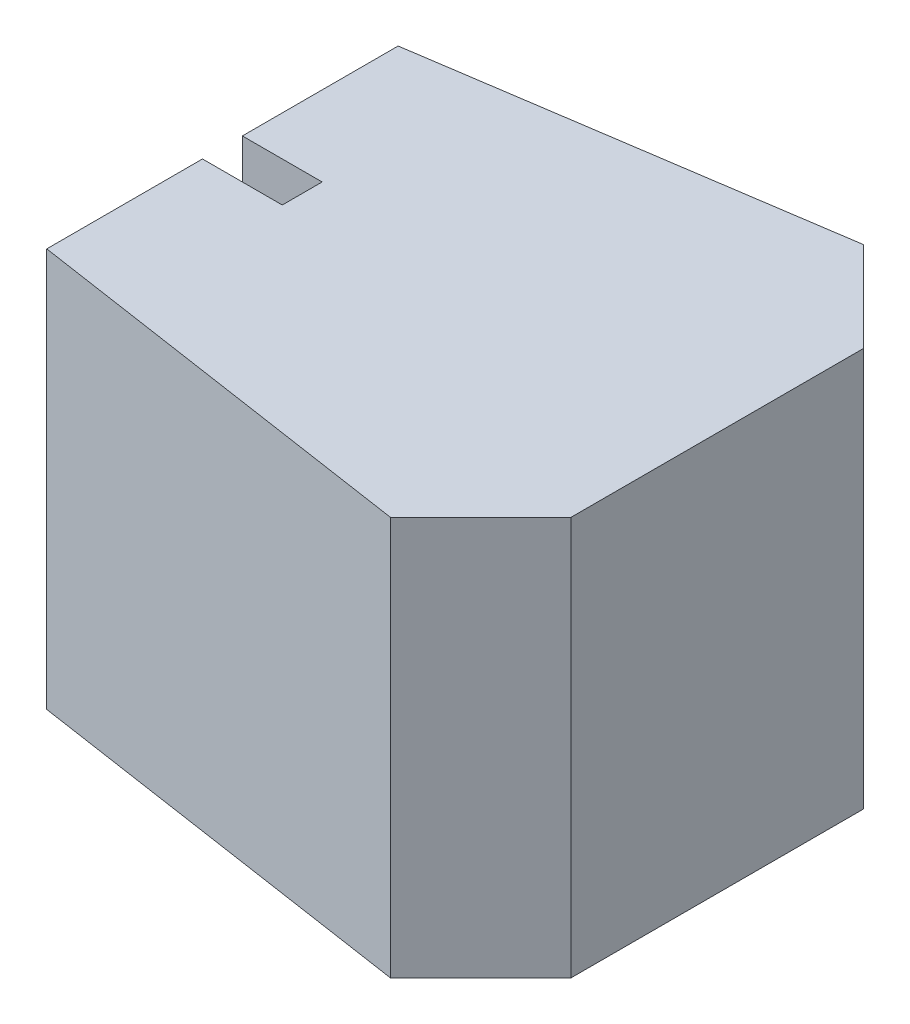
SolidWorks part; units mm, degrees
ref_plane "Front Plane" through (0, 0, 0) normal (0, 0, 1) x (1, 0, 0)
ref_plane "Top Plane" through (0, 0, 0) normal (0, 1, 0) x (1, 0, 0)
ref_plane "Right Plane" through (0, 0, 0) normal (1, 0, 0) x (0, 0, -1)
sketch "Sketch1" plane through (0, 0, 0) normal (0, 1, 0) x (1, 0, 0)
  line L0 (0, 0) -> (600, 0) construction
  line L1 (0, -200) -> (0, 200) construction
  line L2 (600, -175) -> (600, 175) construction
  line L3 (600, 175) -> (500, 275) construction
  line L4 (500, 275) -> (0, 200) construction
  line L5 (100, -25) -> (100, 25)
  line L6 (100, 25) -> (0, 25)
  line L7 (100, -25) -> (0, -25)
  line L8 (500, -275) -> (0, -200) construction
  line L9 (600, -175) -> (500, -275) construction
  line L10 (507.0092, -296.2751) -> (-20, -217.2237)
  line L11 (-20, -217.2237) -> (-20, 217.2237)
  line L12 (507.0092, 296.2751) -> (-20, 217.2237)
  line L13 (620, 183.2843) -> (507.0092, 296.2751)
  line L14 (620, -183.2843) -> (620, 183.2843)
  line L15 (620, -183.2843) -> (507.0092, -296.2751)
  line L16 (0, 200) -> (0, 220.2237)
  line L17 (0, -200) -> (0, -220.2237)
  line L18 (0, 200) -> (0, 25)
  line L19 (0, -25) -> (0, -200)
  point P6 (0, 0)
  point P8 (600, 0)
  point P13 (100, 0)
  dimension "D1" = 600
  dimension "D2" = 400
  dimension "D3" = 350
  dimension "D4" = 100
  dimension "D5" = 75
  dimension "D6" = 50
  dimension "D7" = 100
  dimension "D8" = 20
extrude "Boss-Extrude1" add sketch "Sketch1" along normal blind 500 contours L7 L19 L17 L10 L15 L14 L13 L12 L16 L18 L6 L5
